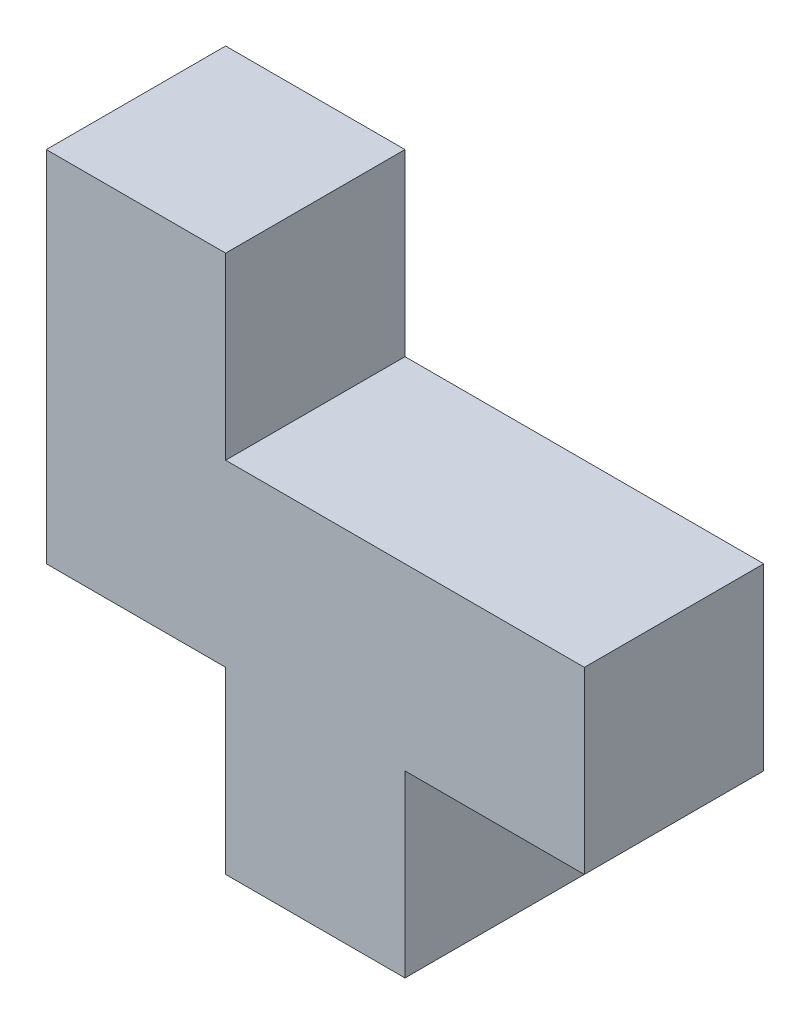
SolidWorks part; units mm, degrees
ref_plane "Front Plane" through (0, 0, 0) normal (0, 0, 1) x (1, 0, 0)
ref_plane "Top Plane" through (0, 0, 0) normal (0, 1, 0) x (1, 0, 0)
ref_plane "Right Plane" through (0, 0, 0) normal (1, 0, 0) x (0, 0, -1)
sketch "Sketch1" plane through (0, 0, 0) normal (0, 0, 1) x (1, 0, 0)
  line L103 (50.8, 0) -> (50.8, 25.4)
  line L104 (50.8, 25.4) -> (76.2, 25.4)
  line L105 (76.2, 25.4) -> (76.2, 50.8)
  line L106 (76.2, 50.8) -> (25.4, 50.8)
  line L107 (25.4, 50.8) -> (25.4, 76.2)
  line L108 (25.4, 76.2) -> (0, 76.2)
  line L109 (0, 76.2) -> (0, 25.4)
  line L110 (0, 25.4) -> (25.4, 25.4)
  line L111 (25.4, 25.4) -> (25.4, 0)
  line L112 (25.4, 0) -> (50.8, 0)
extrude "Boss-Extrude1" add sketch "Sketch1" along normal blind 25.4
